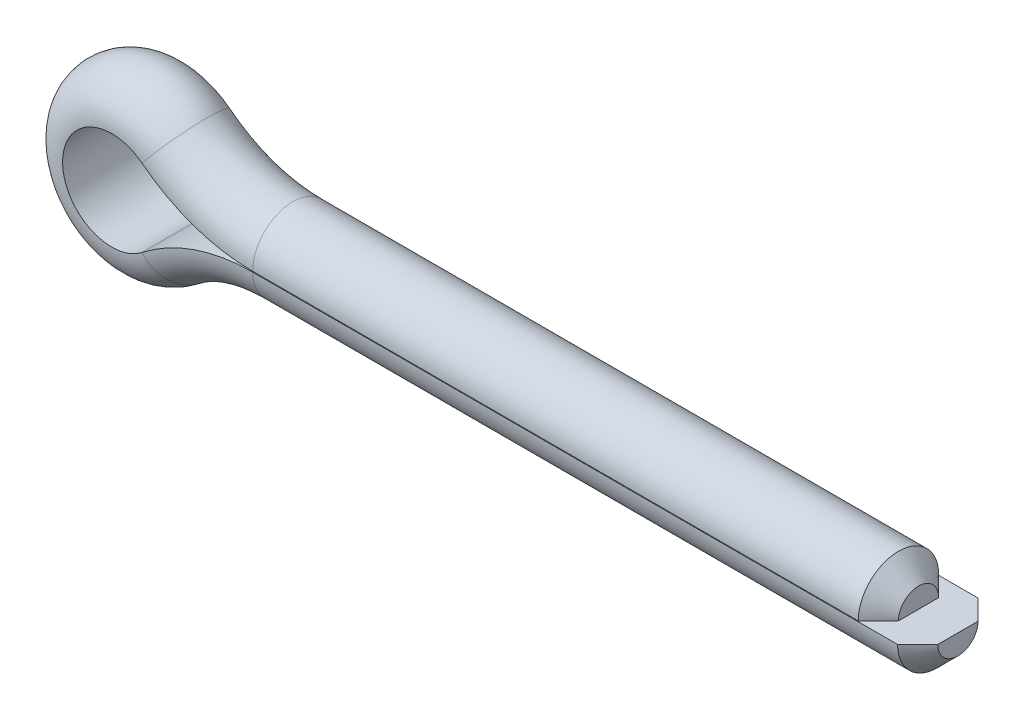
SolidWorks part; units mm, degrees
material "ASTM A36 Steel"
ref_plane "Front" through (0, 0, 0) normal (0, 0, 1) x (1, 0, 0)
ref_plane "Top" through (0, 0, 0) normal (0, 1, 0) x (1, 0, 0)
ref_plane "Right" through (0, 0, 0) normal (1, 0, 0) x (0, 0, -1)
sketch "Sketch1" plane through (0, 0, 0) normal (0, 0, 1) x (1, 0, 0)
  line L0 (-54.4631, 0) -> (2.794, 0) construction
  line L1 (-44.45, -0.0254) -> (2.794, -0.0254)
  line L2 (-50.9706, 0.0254) -> (2.794, 0.0254) construction
  line L3 (-44.45, 0.0254) -> (0, 0.0254)
  line L4 (-11.4985, 0.0254) -> (2.794, 0.0254) construction
  line L5 (-11.4985, -0.0254) -> (2.794, -0.0254) construction
  line L6 (-54.4631, 3.4925) -> (-54.4631, 0.635) construction
  line L7 (-54.4631, 3.4925) -> (-54.4631, 6.35) construction
  line L8 (-11.4985, 0) -> (2.794, 0) construction
  line L9 (0, 0.0254) -> (0, 0) construction
  line L10 (-54.4631, 0) -> (-54.4631, -6.35) construction
  arc A1 (-52.3034, 2.7447) -> (-52.3034, -2.7447) centre (-54.4631, 0) ccw
  arc A2 (-44.45, -0.0254) -> (-52.3034, -2.7447) centre (-44.45, -12.7254) ccw
  arc A3 (-52.3034, 2.7447) -> (-44.45, 0.0254) centre (-44.45, 12.7254) ccw
  circle A4 centre (-54.4631, 0) radius 6.35 construction
  point P15 (0, 0.0254)
  point P24 (0, 0)
  dimension "D6" = 12.7
  dimension "D4" = 0.0254
  dimension "D5" = 0.0254
sketch "Sketch2" plane through (0, 0, 0) normal (1, 0, 0) x (0, 0, -1)
  line L0 (-2.8575, 0.0254) -> (2.8575, 0.0254)
  arc A0 (2.8575, 0.0254) -> (-2.8575, 0.0254) centre (0, 0.0254) ccw
sweep "Sweep1" add profiles "Sketch2" path "Sketch1"
chamfer "Chamfer1" distance 1.4287 angle 45 2 edges at (2.794, -2.8829, 0) (0, 2.8829, 0)
equation "\"D6@Sketch1\" = \"HeadOD@Sketch1\""
equation "\"WireWidth@Sketch2\" = \"WireWidth@Sketch1\""
equation "\"D1@Chamfer1\" = \"WireWidth@Sketch1\"*.25"
